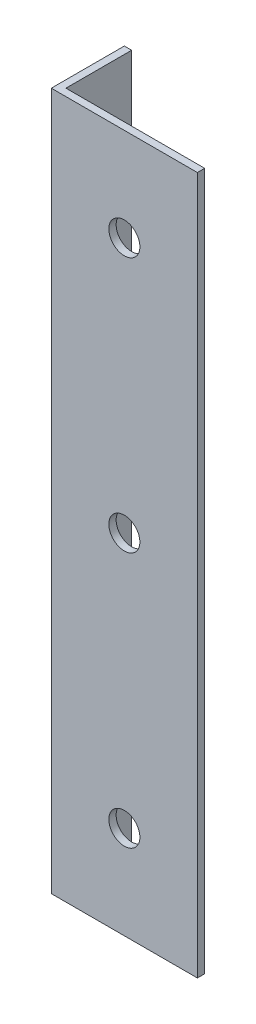
SolidWorks part; units mm, degrees
material "1060 Сплав"
ref_plane "Спереди" through (0, 0, 0) normal (0, 0, 1) x (1, 0, 0)
ref_plane "Сверху" through (0, 0, 0) normal (0, 1, 0) x (1, 0, 0)
ref_plane "Справа" through (0, 0, 0) normal (1, 0, 0) x (0, 0, -1)
sketch "Эскиз1" plane through (0, 0, 0) normal (0, 1, 0) x (1, 0, 0)
  line L0 (0, 0) -> (0, 20)
  line L1 (0, 20) -> (2, 20)
  line L2 (2, 20) -> (2, 2)
  line L3 (2, 2) -> (40, 2)
  line L4 (40, 2) -> (40, 0)
  line L5 (40, 0) -> (0, 0)
  dimension "D1" = 2
  dimension "D2" = 40
  dimension "D3" = 20
extrude "Бобышка-Вытянуть1" add sketch "Эскиз1" along normal blind 191
sketch "Эскиз2" plane through (0, 0, 0) normal (0, 0, 1) x (1, 0, 0)
  line L0 (20, 191) -> (20, 0) construction
  line L1 (0, 191) -> (40, 191) construction
  line L2 (0, 0) -> (40, 0) construction
  line L3 (40, 95.5) -> (0, 95.5) construction
  line L4 (40, 191) -> (40, 0) construction
  line L5 (0, 191) -> (0, 0) construction
  circle A1 centre (20, 165.5) radius 4.25
  circle A2 centre (20, 95.5) radius 4.25
  circle A3 centre (20, 25.5) radius 4.25
  dimension "D1" = 70
  dimension "D2" = 70
  dimension "D4" = 8.5
extrude "Вырез-Вытянуть1" cut sketch "Эскиз2" against normal through all
sketch "Эскиз3" plane through (0, 0, 0) normal (-1, 0, 0) x (0, 0, 1)
  circle A0 centre (-10, 12) radius 2.25 construction
  circle A1 centre (-10, 12) radius 2.25
  circle A2 centre (-10, 179) radius 2.25 construction
  circle A3 centre (-10, 179) radius 2.25
extrude "Вырез-Вытянуть2" cut sketch "Эскиз3" against normal through all
